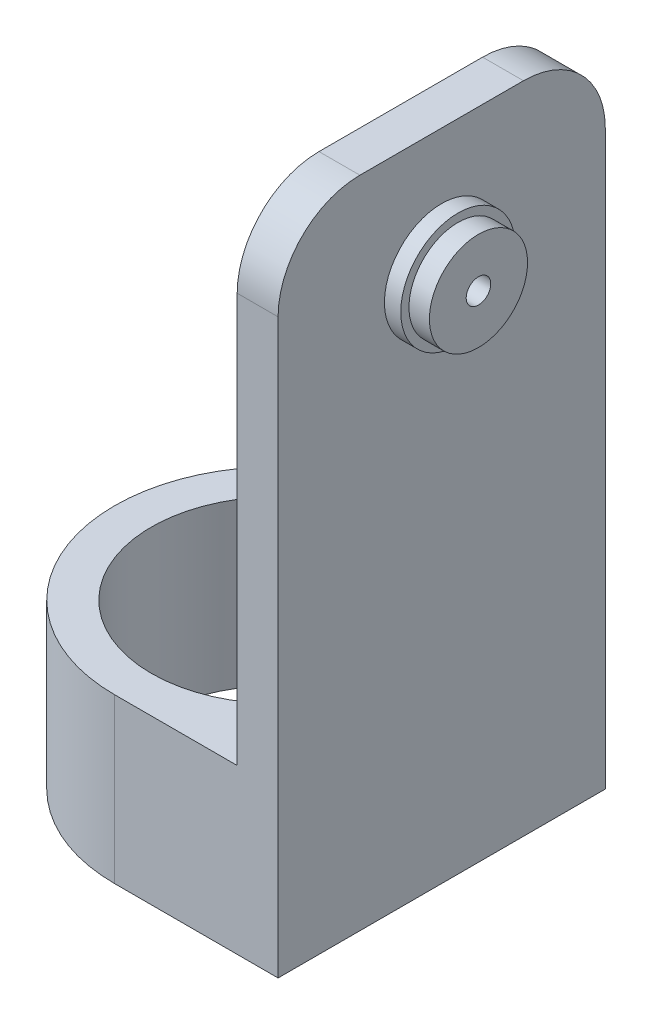
SolidWorks part; units mm, degrees
ref_plane "Спереди" through (0, 0, 0) normal (0, 0, 1) x (1, 0, 0)
ref_plane "Сверху" through (0, 0, 0) normal (0, 1, 0) x (1, 0, 0)
ref_plane "Справа" through (0, 0, 0) normal (1, 0, 0) x (0, 0, -1)
sketch "Эскиз1" plane through (0, 0, 0) normal (0, 1, 0) x (1, 0, 0)
  line L1 (0, 20) -> (20, 20)
  line L3 (0, -20) -> (20, -20)
  line L4 (20, 20) -> (20, -20)
  line L5 (-20, 20) -> (20, -20) construction
  line L6 (-20, -20) -> (20, 20) construction
  circle A0 centre (0, 0) radius 15.5
  arc A1 (0, 20) -> (0, -20) centre (0, 0) ccw
  dimension "D1" = 31
  dimension "D2" = 40
extrude "Бобышка-Вытянуть2" add sketch "Эскиз1" along normal blind 20
sketch "Эскиз2" plane through (0, 20, 0) normal (0, 1, 0) x (1, 0, 0)
  line L1 (20, 20) -> (15, 20)
  line L2 (20, 20) -> (20, -20)
  line L3 (20, -20) -> (15, -20)
  line L4 (15, 20) -> (15, -20)
  dimension "D1" = 40
  dimension "D2" = 5
extrude "Бобышка-Вытянуть3" add sketch "Эскиз2" along normal blind 60
sketch "Эскиз3" plane through (20, 0, 0) normal (1, 0, 0) x (0, 0, -1)
  line L0 (-20, 80) -> (20, 80) construction
  circle A0 centre (0, 65) radius 7
  dimension "D2" = 14
  dimension "D1" = 15
extrude "Бобышка-Вытянуть4" add sketch "Эскиз3" along normal blind 2
sketch "Эскиз4" plane through (22, 0, 0) normal (1, 0, 0) x (0, 0, -1)
  circle A0 centre (0, 65) radius 6
  dimension "D1" = 12
extrude "Бобышка-Вытянуть5" add sketch "Эскиз4" along normal blind 2.5
sketch "Эскиз5" plane through (24.5, 0, 0) normal (1, 0, 0) x (0, 0, -1)
  circle A0 centre (0, 65) radius 1.5
  dimension "D1" = 3
extrude "Вырез-Вытянуть1" cut sketch "Эскиз5" against normal through all
fillet "Скругление1" radius 10 2 edges at (17.5, 80, -20) (17.5, 80, 20)
